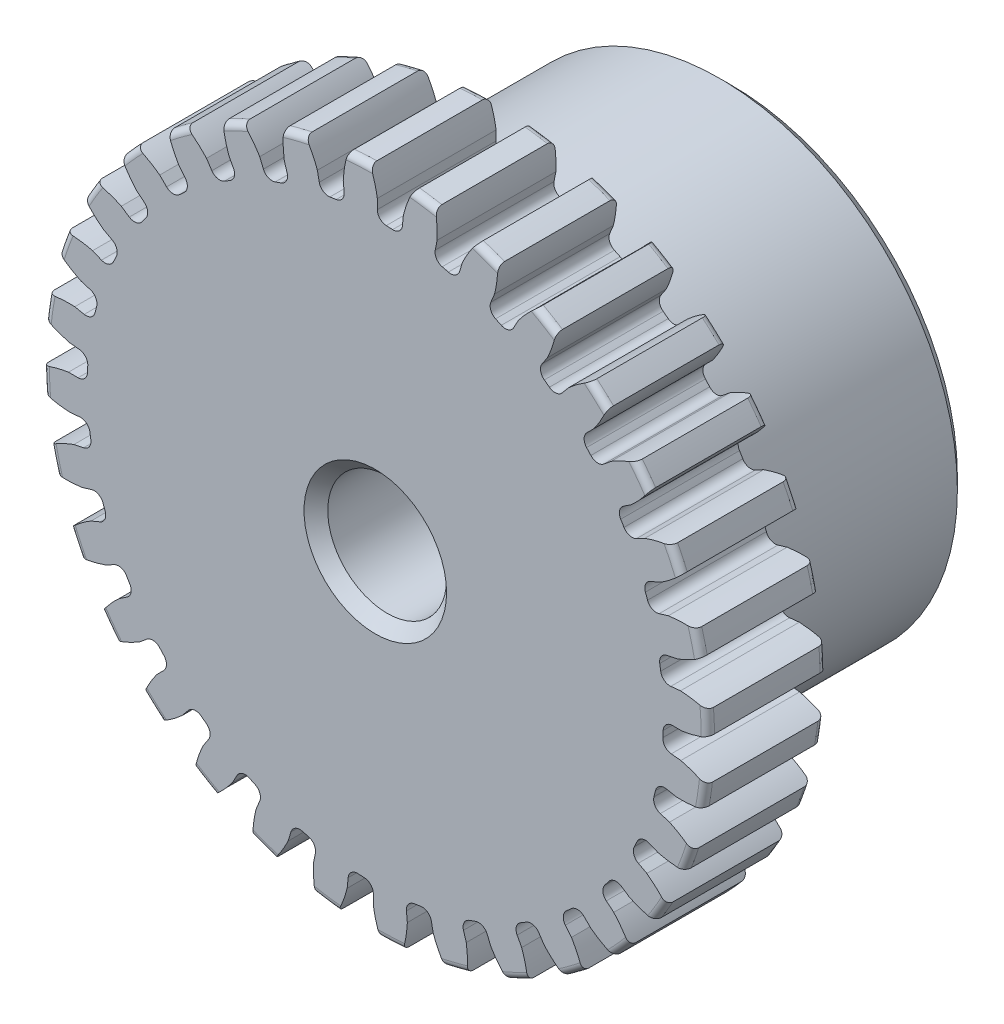
SolidWorks part; units mm, degrees
ref_plane "Front" through (0, 0, 0) normal (0, 0, 1) x (1, 0, 0)
ref_plane "Top" through (0, 0, 0) normal (0, 1, 0) x (1, 0, 0)
ref_plane "Right" through (0, 0, 0) normal (1, 0, 0) x (0, 0, -1)
sketch "Sketch1" plane through (0, 0, 0) normal (0, 0, 1) x (1, 0, 0)
  line L0 (-406.4, 0) -> (406.4, 0) construction
  circle A0 centre (0, 0) radius 8.89
  circle A1 centre (0, 0) radius 8.4709 construction
  circle A3 centre (0, 0) radius 7.6988 construction
  dimension "D1" = 1.1912
  dimension "OD" = 17.78
  dimension "Ptich Dia" = 16.9418
  dimension "Root Dia" = 15.3976
  dimension "D3" = 0.4191
  dimension "Number of Teeth" = 812.8
extrude "Boss-Extrude1" add sketch "Sketch1" against normal blind 3.175
sketch "Sketch2" plane through (0, 0, 0) normal (1, 0, 0) x (0, 0, -1)
  line L0 (3.175, 0) -> (9.525, 0)
  line L1 (3.175, 0) -> (3.175, 6.35)
  line L2 (3.175, 6.35) -> (9.525, 6.35)
  line L3 (9.525, 6.35) -> (9.525, 0)
  point P5 (9.525, -6.35)
  point P6 (0, -8.89)
  point P7 (3.175, -8.89)
  point P9 (0, 8.89)
  dimension "Face Wd" = 3.175
  dimension "B Hub Dia" = 12.7
  dimension "D O'all Lg." = 9.525
revolve "Revolve1" add sketch "Sketch2" angle 360 about L0
fillet "Fillet2" radius 0.1778 3 edges at (8.89, 0, -3.175) (8.89, 0, 0) (6.35, 0, -3.175)
sketch "Sketch3" plane through (0, 0, 0) normal (0, 0, 1) x (1, 0, 0)
  line L0 (0, 0) -> (0, 8.89) construction
  line L1 (-2.0534, 7.9399) -> (0, 8.4709)
  line L2 (-9.5921, 8.4709) -> (9.5921, 8.4709) construction
  line L3 (-9.2865, 6.0692) -> (9.2865, 10.8726) construction
  line L4 (-2.0534, 7.9399) -> (0, 0) construction
  line L5 (-5.2375, 6.3108) -> (0, 0) construction
  line L6 (-5.2375, 6.3108) -> (-0.8504, 9.9518) construction
  line L7 (-1.4318, 8.0751) -> (0, 0) construction
  line L8 (-1.4318, 8.0751) -> (0.03, 8.3343) construction
  arc A0 (-2.0534, 7.9399) -> (-5.2375, 6.3108) centre (0, 0) ccw
  circle A1 centre (0, 0) radius 8.4709 construction
  circle A2 centre (0, 0) radius 8.2011 construction
  arc A3 (-2.0534, 7.9399) -> (-1.4318, 8.0751) centre (0, 0) cw
  circle A4 centre (0, 0) radius 8.89 construction
  point P6 (0, 8.4709)
  dimension "D1" = 2.1209
  dimension "Pressure Angle" = 14.5
  dimension "D2" = 3.6056
  dimension "D3" = 5.7011
  dimension "D4" = 0.6363
  dimension "D5" = 1.4847
sketch "Sketch4" plane through (0, 0, 0) normal (0, 0, 1) x (1, 0, 0)
  line L0 (0, 0) -> (0.4151, 8.4505) construction
  line L1 (0.0531, 8.2009) -> (0.0531, 7.6986)
  line L2 (0, 8.4709) -> (0.8303, 8.4301) construction
  line L3 (0.7509, 8.1666) -> (0.7017, 7.6667)
  line L4 (0.0531, 7.6986) -> (0, 0) construction
  line L5 (0, 0) -> (0, 8.89) construction
  line L6 (-5.2375, 6.3108) -> (-0.8504, 9.9518) construction
  line L7 (-5.2375, 6.3108) -> (-0.8504, 9.9518) construction
  arc A0 (0.7017, 7.6667) -> (0.0531, 7.6986) centre (0, 0) ccw
  arc A1 (0, 8.4709) -> (0.8303, 8.4301) centre (0, 0) cw construction
  circle A2 centre (0, 0) radius 8.4709 construction
  circle A3 centre (0, 0) radius 8.2011 construction
  circle A4 centre (0, 0) radius 7.6988 construction
  arc A5 (1.8218, 9.8205) -> (-0.8504, 9.9518) centre (0, 0) ccw
  spline S0 degree 2 poles (-0.8504, 9.9518) (-0.0946, 9.1822) (0.0531, 8.2009) knots 0 0 0 1 1 1
  spline S1 degree 2 poles (1.8218, 9.8205) (0.9942, 9.1287) (0.7509, 8.1666) knots 0 0 0 1 1 1
  dimension "D1" = 0.8316
extrude "Cut-Extrude1" cut sketch "Sketch4" against normal through all
fillet "Fillet1" radius 0.2495 2 edges at (0.7017, 7.6667, -1.5875) (0.0531, 7.6986, -1.5875)
pattern_circular "CirPattern1" count 32 over 360 about axis through (0, 0, -3.175) along (0, 0, 1) of "Cut-Extrude1", "Fillet1"
sketch "Sketch5" plane through (0, 0, 0) normal (0, 0, 1) x (1, 0, 0)
  circle A0 centre (0, 0) radius 1.5875
  circle A1 centre (0, 0) radius 1.5875 construction
  dimension "Bore Min" = 3.175
  dimension "Bore Max" = 3.175
extrude "Cut-Extrude2" cut sketch "Sketch5" against normal through all
chamfer "Chamfer1" distance 0.3175 angle 45 3 edges at (6.35, 0, -9.525) (1.5875, 0, 0) (1.5875, 0, -9.525)
sketch "Pitch Dia" plane through (0, 0, 0) normal (0, 0, 1) x (1, 0, 0)
  circle A0 centre (0, 0) radius 8.4709 construction
  circle A1 centre (0, 0) radius 8.4709 construction
equation "\"D1@Boss-Extrude1\" = \"Face Wd@Sketch2\""
equation "\"D2@Sketch3\" = \"D1@Sketch3\"*1.7"
equation "\"D3@Sketch3\" = \"D1@Sketch3\"+\"D2@Sketch3\"-.001"
equation "\"D4@Sketch3\" = \"D1@Sketch3\"*.3"
equation "\"D5@Sketch3\" = \"D1@Sketch3\"-\"D4@Sketch3\""
equation "\"D1@Sketch4\" = 1.5708/(\"Number of Teeth@Sketch1\"/\"Ptich Dia@Sketch1\")"
equation "\"D1@Chamfer1\" = \"B Hub Dia@Sketch2\"*.025"
equation "\"D1@CirPattern1\" = \"Number of Teeth@Sketch1\""
equation "\"D1@Fillet1\" = \"D1@Sketch4\"*.3"
equation "\"D1@Fillet2\" = \"OD@Sketch1\"*.01"
equation "\"D1@Sketch1\" = 2.250/(\"Number of Teeth@Sketch1\"/\"Ptich Dia@Sketch1\")"
